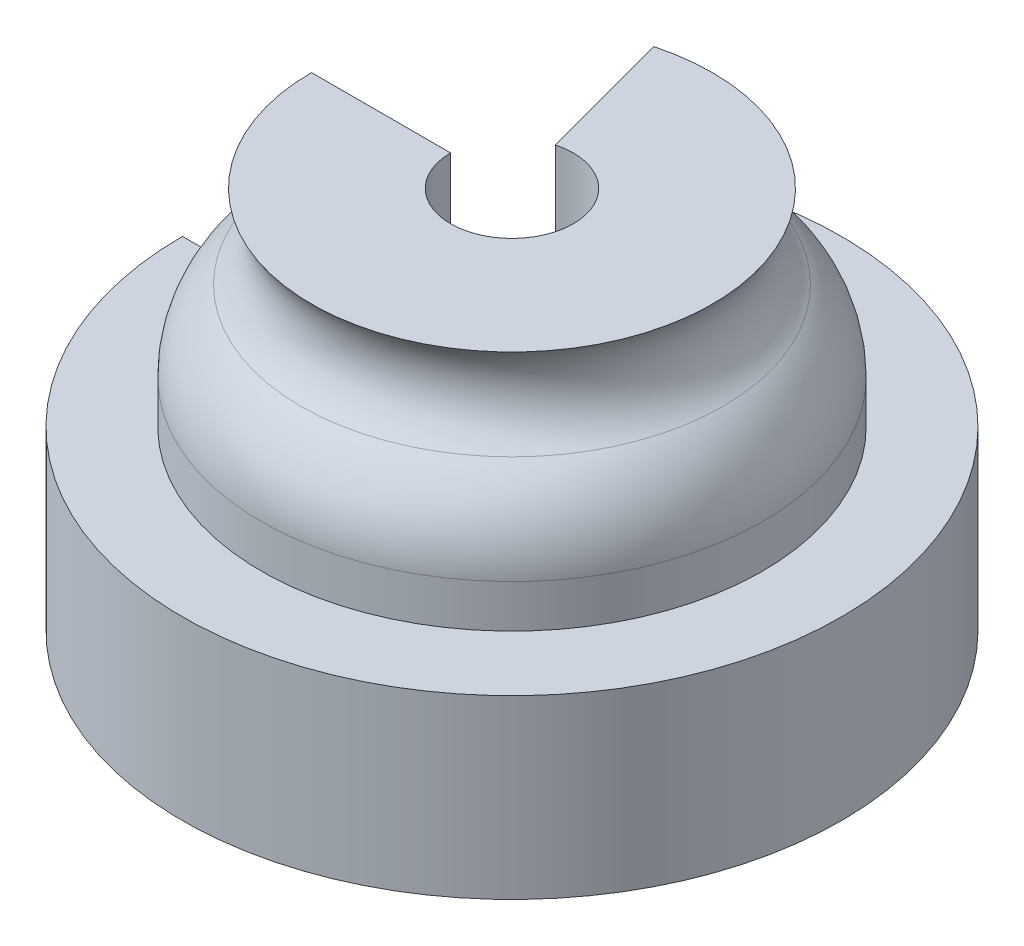
SolidWorks part; units mm, degrees
ref_plane "前视基准面" through (0, 0, 0) normal (0, 0, 1) x (1, 0, 0)
ref_plane "上视基准面" through (0, 0, 0) normal (0, 1, 0) x (1, 0, 0)
ref_plane "右视基准面" through (0, 0, 0) normal (1, 0, 0) x (0, 0, -1)
sketch "Sketch1" plane through (0, 0, 0) normal (0, 0, 1) x (1, 0, 0)
  line L0 (0, 0) -> (0, 34.2118) construction
  line L1 (-10.7468, 0) -> (-10.7468, 34.0911)
  line L2 (-10.7468, 34.0911) -> (-16.6651, 34.0911)
  line L3 (-23.5385, 20.1246) -> (-23.5385, 11.4039)
  line L4 (-23.5385, 11.4039) -> (-32.2272, 11.4039)
  line L5 (-32.2272, 11.4039) -> (-32.2272, 0)
  line L6 (-32.2272, 0) -> (-10.7468, 0)
  arc A0 (-16.6651, 34.0911) -> (-20.7629, 25.7645) centre (-27.1739, 34.0911) cw
  arc A1 (-20.7629, 25.7645) -> (-23.5385, 20.1246) centre (-16.4206, 20.1246) ccw
  point P10 (0, 0)
  point P14 (-19.4355, 26.7299)
  point P15 (-21.9697, 13.0934)
  point P16 (-32.2272, 11.4039)
  point P17 (0, 0)
  point P18 (-23.5385, 20.2133)
  point P19 (0, 0)
  point P20 (-18.7114, 34.0911)
  point P21 (0, 0)
  point P22 (0, 0)
  point P23 (0, 0)
  point P24 (0, 0)
  point P25 (-20.7629, 25.7645)
revolve "Revolve-Thin1" add sketch "Sketch1" angle 285 about L0
